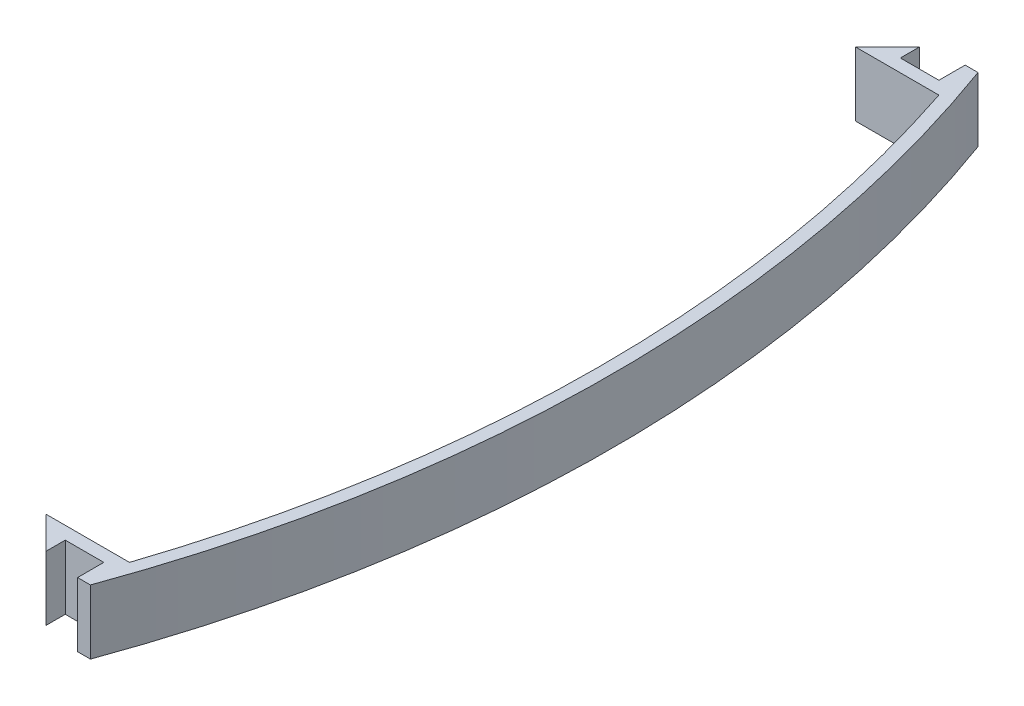
SolidWorks part; units mm, degrees
ref_plane "Plan de face" through (0, 0, 0) normal (0, 0, 1) x (1, 0, 0)
ref_plane "Plan de dessus" through (0, 0, 0) normal (0, 1, 0) x (1, 0, 0)
ref_plane "Plan de droite" through (0, 0, 0) normal (1, 0, 0) x (0, 0, -1)
sketch "Esquisse1" plane through (0, 0, 0) normal (0, 1, 0) x (1, 0, 0)
  line L0 (0, 73.119) -> (0, -80.3873) construction
  line L1 (0, -61) -> (-13, -61)
  line L2 (-13, -61) -> (-8, -66)
  line L3 (-8, -66) -> (-8, -63)
  line L4 (-8, -63) -> (-2, -63)
  line L5 (-2, -63) -> (-2, -67.0869)
  line L6 (0, -67.0869) -> (-2, -67.0869)
  line L7 (0, 71.0869) -> (-2, 71.0869)
  line L13 (0, 65) -> (-13, 65)
  line L14 (-13, 65) -> (-8, 70)
  line L15 (-8, 70) -> (-8, 67)
  line L16 (-8, 67) -> (-2, 67)
  line L17 (-2, 67) -> (-2, 71.0869)
  arc A0 (0, 65) -> (0, -61) centre (-189.8183, 2) cw
  arc A1 (0, -67.0869) -> (0, 71.0869) centre (-189.8183, 2) ccw
  dimension "D9" = 2
  dimension "D10" = 200
  dimension "D1" = 65
  dimension "D2" = 126
  dimension "D3" = 2
  dimension "D4" = 3
  dimension "D5" = 13
  dimension "D6" = 6
  dimension "D7" = 5
  dimension "D17" = 13
  dimension "D18" = 6
  dimension "D19" = 3
  dimension "D21" = 5
  dimension "D22" = 2
extrude "Boss.-Extru.1" add sketch "Esquisse1" along normal blind 10
